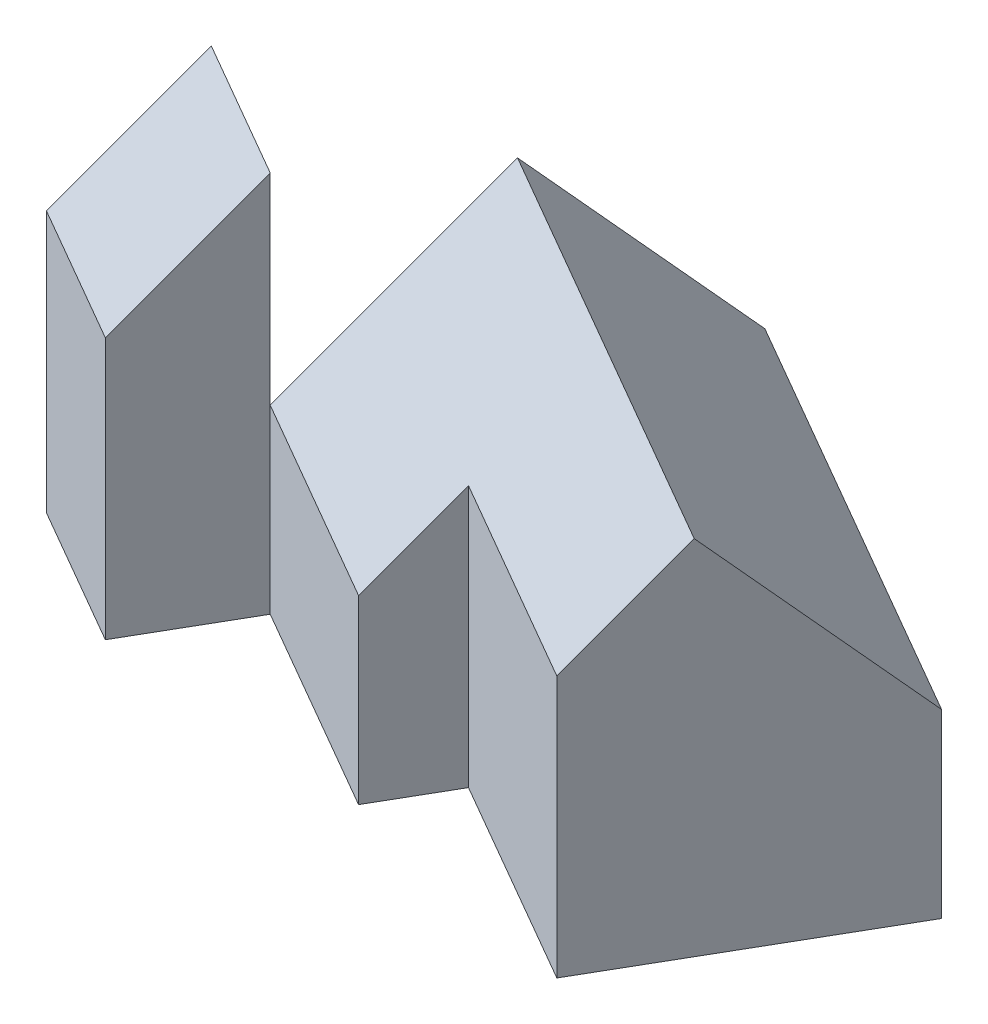
SolidWorks part; units mm, degrees
other "Perspective"
ref_plane "Front Plane" through (0, 0, 0) normal (0, 0, 1) x (1, 0, 0)
ref_plane "Top Plane" through (0, 0, 0) normal (0, 1, 0) x (1, 0, 0)
ref_plane "Right Plane" through (0, 0, 0) normal (1, 0, 0) x (0, 0, -1)
sketch "Sketch1" plane through (0, 0, 0) normal (0, 1, 0) x (1, 0, 0)
  line L0 (0, 0) -> (35, 60.6218)
  line L1 (35, 60.6218) -> (-68.923, 120.6218)
  line L2 (-68.923, 120.6218) -> (-113.923, 42.6795)
  line L3 (-113.923, 42.6795) -> (-61.9615, 12.6795)
  line L4 (-61.9615, 12.6795) -> (-51.9615, 30)
  line L5 (-51.9615, 30) -> (0, 0)
  line L6 (-113.923, 42.6795) -> (-128.923, 16.6987)
  line L7 (-128.923, 16.6987) -> (-163.5641, 36.6987)
  line L8 (-163.5641, 36.6987) -> (-148.5641, 62.6795)
  line L9 (-148.5641, 62.6795) -> (-113.923, 42.6795)
  line L10 (0, 0) -> (111.9401, 0) construction
  dimension "D1" = 70
  dimension "D2" = 60
  dimension "D3" = 60
  dimension "D4" = 20
  dimension "D5" = 40
  dimension "D6" = 30
  dimension "D7" = 60
extrude "Extrude1" add sketch "Sketch1" along normal blind 95 contours L9 L8 L7 L6 | L4 L5 L0 L1 L2 L3
sketch "Sketch2" plane through (0, 0, 0) normal (0.866, 0, 0.5) x (0.5, 0, -0.866)
  line L0 (70, 95) -> (-20, 95)
  line L1 (-20, 95) -> (-20, 84.7708)
  line L2 (-20, 95) -> (-20, 0) construction
  line L3 (25, 90) -> (70, 45)
  line L4 (70, 95) -> (70, 0) construction
  line L5 (70, 45) -> (70, 95)
  line L6 (-20, 45) -> (25, 90)
  line L7 (-20, 84.7708) -> (-20, 45)
  line L8 (-20, 0) -> (0, 0) construction
  dimension "D1" = 5
  dimension "D2" = 45
  dimension "D3" = 45
  dimension "D4" = 45
extrude "Extrude2" cut sketch "Sketch2" against normal blind 125
sketch "Sketch3" plane through (-103.923, 0, -60) normal (0.866, 0, 0.5) x (0.5, 0, -0.866)
  line L0 (-50, 65) -> (-20, 95)
  line L1 (-50, 95) -> (-50, 0) construction
  line L2 (-20, 95) -> (-50, 95)
  line L3 (-50, 95) -> (-50, 65)
  dimension "D1" = 30
extrude "Extrude3" cut sketch "Sketch3" against normal blind 125
